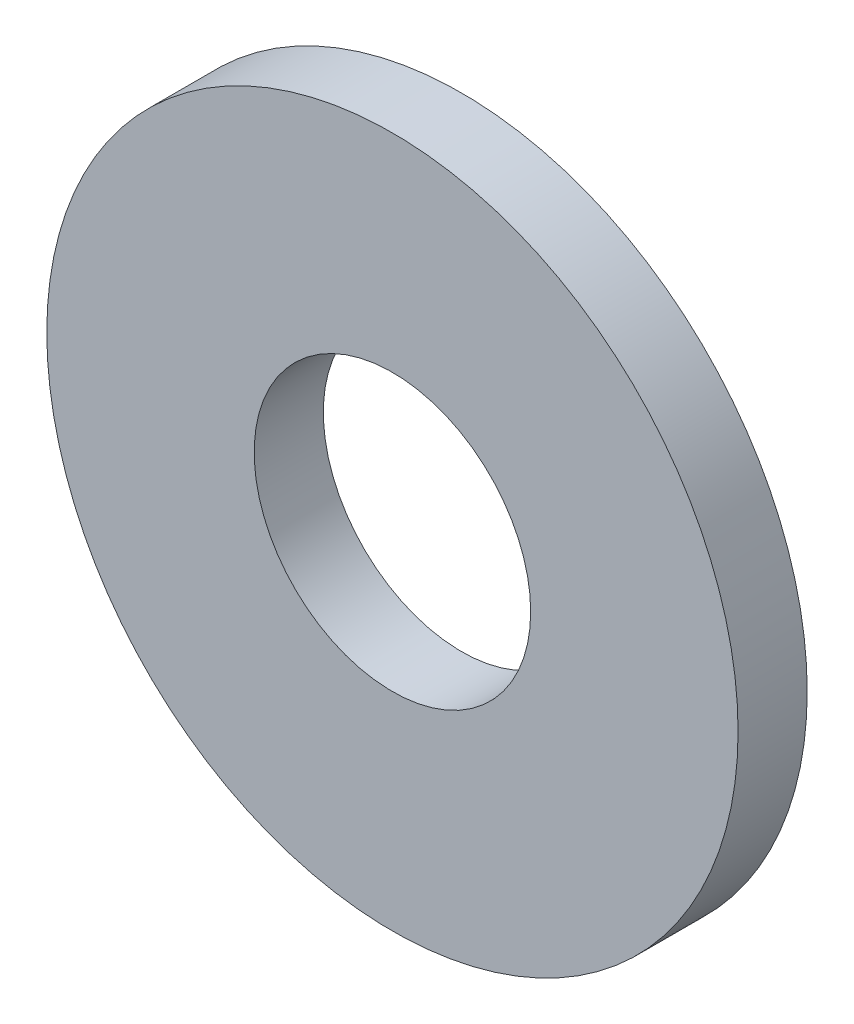
SolidWorks part; units mm, degrees
ref_plane "Front Plane" through (0, 0, 0) normal (0, 0, 1) x (1, 0, 0)
ref_plane "Top Plane" through (0, 0, 0) normal (0, 1, 0) x (1, 0, 0)
ref_plane "Right Plane" through (0, 0, 0) normal (1, 0, 0) x (0, 0, -1)
sketch "Sketch1" plane through (0, 0, 0) normal (0, 0, 1) x (1, 0, 0)
  circle A0 centre (0, 0) radius 3.175
  circle A1 centre (0, 0) radius 7.9375
  dimension "D1" = 15.875
  dimension "D2" = 6.35
extrude "Boss-Extrude1" add sketch "Sketch1" along normal blind 1.5875
